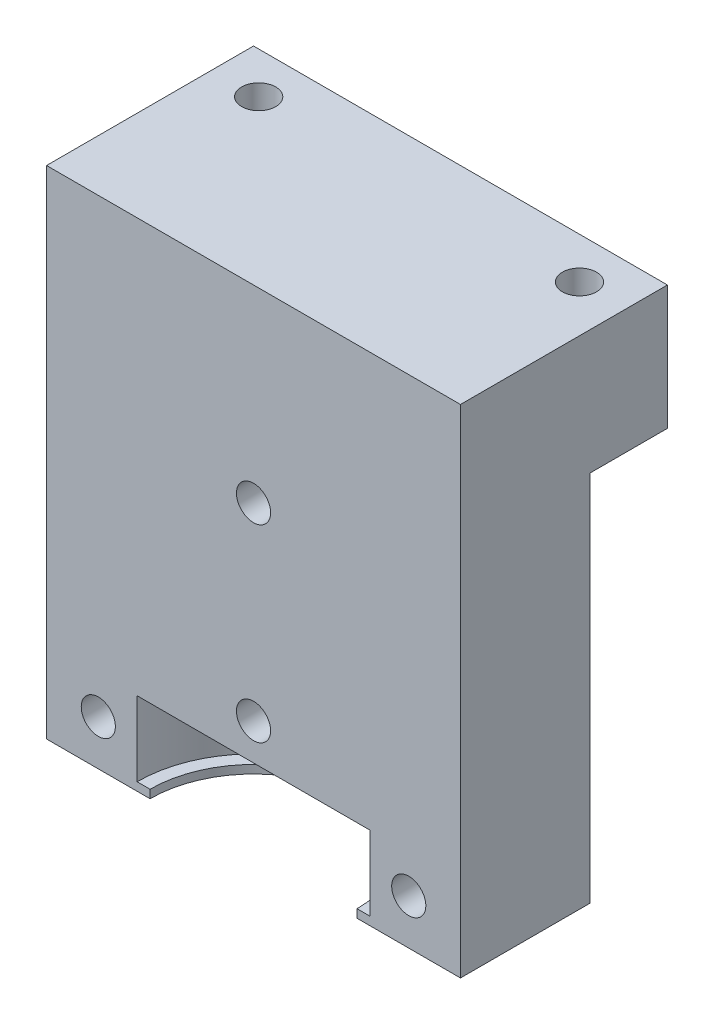
SolidWorks part; units mm, degrees
ref_plane "Front Plane" through (0, 0, 0) normal (0, 0, 1) x (1, 0, 0)
ref_plane "Top Plane" through (0, 0, 0) normal (0, 1, 0) x (1, 0, 0)
ref_plane "Right Plane" through (0, 0, 0) normal (1, 0, 0) x (0, 0, -1)
sketch "Sketch1" plane through (0, 0, 0) normal (0, 1, 0) x (1, 0, 0)
  line L1 (20, 20) -> (-20, 20)
  line L2 (20, 20) -> (20, -20)
  line L3 (20, -20) -> (-20, -20)
  line L4 (-20, 20) -> (-20, -20)
  line L5 (0, -20) -> (0, 20) construction
  line L6 (20, 0) -> (-20, 0) construction
  point P0 (0, 0)
extrude "Boss-Extrude1" add sketch "Sketch1" against normal blind 48
hole_wizard "M4x0.7 Tapped Hole1" positions "Sketch2" profile "Sketch3" tap size "M4x0.7" standard "ANSI Metric" end condition through all
sketch "Sketch2" plane through (0, 0, 0) normal (0, 1, 0) x (1, 0, 0)
  line L1 (-15.5, -16) -> (15.5, -16)
  line L2 (-15.5, -16) -> (-15.5, 16)
  line L3 (-15.5, 16) -> (15.5, 16)
  line L4 (15.5, -16) -> (15.5, 16)
  line L5 (15.5, 0) -> (0, 0) construction
  line L6 (0, 0) -> (0, -16) construction
  point P2 (-15.5, 16)
  point P4 (15.5, 16)
  point P6 (15.5, -16)
  point P8 (-15.5, -16)
  dimension "D1" = 31
  dimension "D2" = 32
sketch "Sketch3" plane through (-15.5, 0, -16) normal (1, 0, 0) x (0, 0, 1)
  line L0 (0, 0) -> (0, 48)
  line L1 (0, 48) -> (1.65, 48)
  line L2 (1.65, 48) -> (1.65, 0)
  line L5 (1.65, 0) -> (0, 0)
  line L11 (0, -6.35) -> (0, 107.95) construction
  dimension "Thread Major Dia." = 3.3
  dimension "Thru Tap Drill Depth" = 48
sketch "Sketch10" plane through (0, 0, 0) normal (0, 1, 0) x (1, 0, 0)
  line L0 (20, -20) -> (20, 20) construction
  line L1 (-20, -20) -> (20, -20)
  line L2 (-20, -20) -> (-20, 0)
  line L3 (-20, 0) -> (20, 0)
  line L4 (20, -20) -> (20, 0)
extrude "Cut-Extrude4" cut sketch "Sketch10" against normal through all
sketch "Sketch11" plane through (0, 0, 0) normal (0, 0, 1) x (1, 0, 0)
  line L0 (0, 0) -> (0, -40) construction
  line L1 (0, -40) -> (11.25, -40)
  line L2 (0, -40) -> (0, -47.2)
  line L3 (0, -47.2) -> (11.25, -47.2)
  line L4 (11.25, -40) -> (11.25, -47.2)
  line L5 (20, 0) -> (-20, 0) construction
  dimension "D1" = 40
  dimension "D2" = 7.2
  dimension "D3" = 22.5
revolve "Cut-Revolve2" cut sketch "Sketch11" angle 360 about L0
sketch "Sketch12" plane through (0, -48, 0) normal (0, -1, 0) x (1, 0, 0)
  line L0 (20, 0) -> (-20, 0) construction
  circle A0 centre (0, 0) radius 10
  dimension "D1" = 20
extrude "Cut-Extrude5" cut sketch "Sketch12" against normal up to next
hole_wizard "M4x0.7 Tapped Hole2" positions "Sketch13" profile "Sketch14" tap size "M4x0.7" standard "ANSI Metric" end condition through all
sketch "Sketch13" plane through (0, 0, -20) normal (0, 0, -1) x (-1, 0, 0)
  line L0 (-15, -43.6281) -> (15, -43.6281) construction
  line L3 (0, -43.6281) -> (0, -36.4844) construction
  line L4 (0, -36.4844) -> (0, -18.2422) construction
  line L5 (0, -18.2422) -> (0, 0) construction
  line L8 (10, -47.2) -> (-10, -47.2) construction
  point P8 (15, -43.6281)
  point P10 (-15, -43.6281)
  point P12 (0, -36.4844)
  point P14 (0, -18.2422)
  dimension "D1" = 30
  dimension "D2" = 3.5719
  dimension "D3" = 7.1437
sketch "Sketch14" plane through (-15, -43.6281, -20) normal (1, 0, 0) x (0, 1, 0)
  line L0 (0, 0) -> (0, 20)
  line L1 (0, 20) -> (1.65, 20)
  line L2 (1.65, 20) -> (1.65, 0)
  line L5 (1.65, 0) -> (0, 0)
  line L11 (0, -6.35) -> (0, 107.95) construction
  dimension "Thru Tap Drill Dia." = 3.3
  dimension "Thru Tap Drill Depth" = 20
cosmetic thread "Hole Thread1" parameters "D2"=4
cosmetic thread "Hole Thread2" parameters "D2"=4
cosmetic thread "Hole Thread3" parameters "D2"=4
cosmetic thread "Hole Thread4" parameters "D2"=4
sketch "Sketch15" plane through (0, -48, 0) normal (0, -1, 0) x (1, 0, 0)
  line L1 (-20, -12.5) -> (20, -12.5)
  line L2 (-20, -12.5) -> (-20, -20)
  line L3 (-20, -20) -> (20, -20)
  line L4 (20, -12.5) -> (20, -20)
  line L5 (-20, -20) -> (-20, 0) construction
  dimension "D1" = 7.5
extrude "Cut-Extrude6" cut sketch "Sketch15" against normal blind 36
